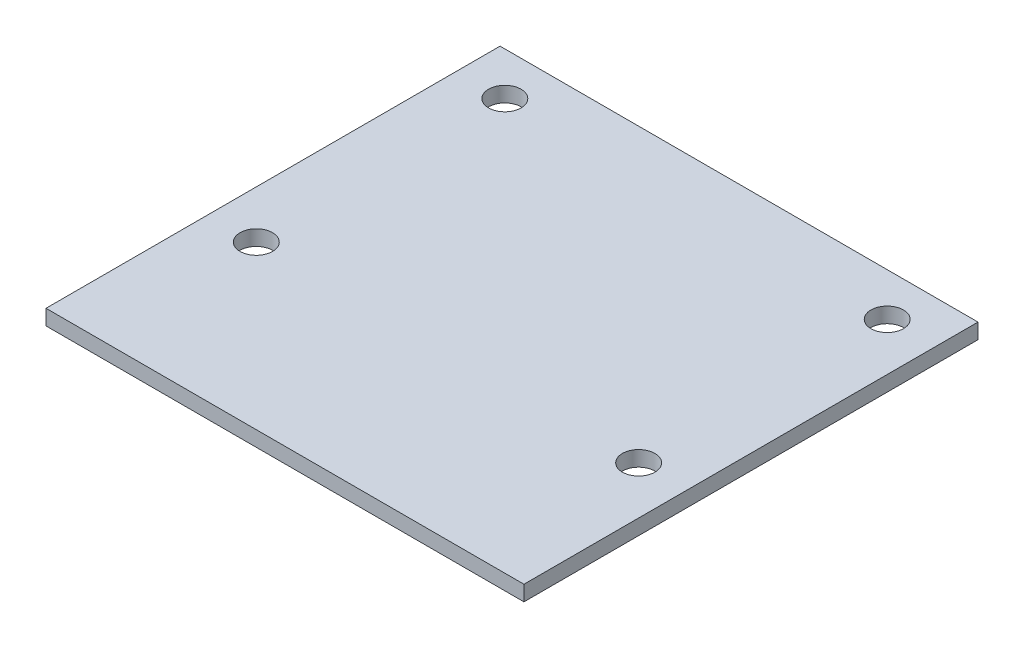
SolidWorks part; units mm, degrees
ref_plane "Front Plane" through (0, 0, 0) normal (0, 0, 1) x (1, 0, 0)
ref_plane "Top Plane" through (0, 0, 0) normal (0, 1, 0) x (1, 0, 0)
ref_plane "Right Plane" through (0, 0, 0) normal (1, 0, 0) x (0, 0, -1)
sketch "Sketch1" plane through (0, 0, 0) normal (0, 1, 0) x (1, 0, 0)
  line L1 (0, 0) -> (50, 0)
  line L2 (0, 0) -> (0, 47.5)
  line L3 (0, 47.5) -> (50, 47.5)
  line L4 (50, 0) -> (50, 47.5)
  circle A0 centre (5, 17) radius 1.7
  circle A1 centre (5, 43) radius 1.7
  circle A2 centre (45, 17) radius 1.7
  circle A3 centre (45, 43) radius 1.7
  dimension "D5" = 3.4
  dimension "D6" = 26
  dimension "D1" = 47.5
  dimension "D2" = 50
  dimension "D3" = 17
  dimension "D4" = 5
  dimension "D7" = 5
extrude "Boss-Extrude1" add sketch "Sketch1" along normal blind 1.6
sketch "Sketch2" plane through (0, 1.6, 0) normal (0, 1, 0) x (1, 0, 0)
  line L0 (0, 0) -> (50, 0) construction
  line L2 (50, 0) -> (50, 47.5) construction
  circle A0 centre (17, 18.5) radius 3
  circle A1 centre (27, 18.5) radius 3
  circle A2 centre (37, 18.5) radius 3
  circle A3 centre (27, 28.5) radius 3
  circle A4 centre (37, 28.5) radius 3
  circle A5 centre (27, 38.5) radius 3
  circle A6 centre (37, 38.5) radius 3
  circle A7 centre (17, 28.5) radius 3
  circle A8 centre (17, 38.5) radius 3
  dimension "D1" = 6
  dimension "D4" = 18.5
  dimension "D5" = 13
  dimension "D2" = 3
  dimension "D3" = 3
